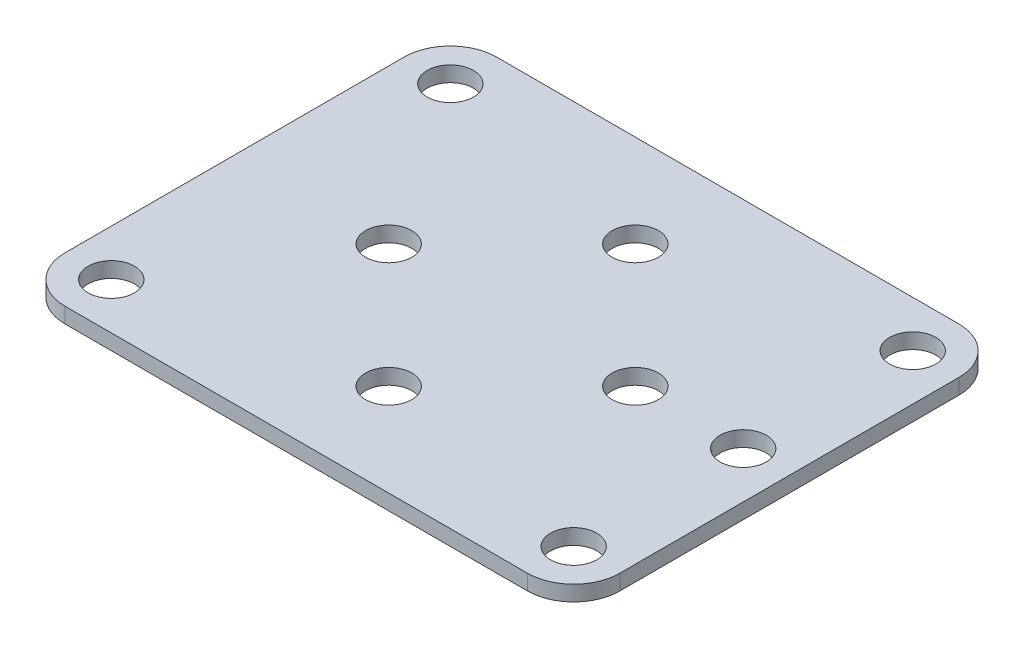
SolidWorks part; units mm, degrees
ref_plane "Front Plane" through (0, 0, 0) normal (0, 0, 1) x (1, 0, 0)
ref_plane "Top Plane" through (0, 0, 0) normal (0, 1, 0) x (1, 0, 0)
ref_plane "Right Plane" through (0, 0, 0) normal (1, 0, 0) x (0, 0, -1)
sketch "Sketch1" plane through (0, 0, 0) normal (0, 1, 0) x (1, 0, 0)
  line L0 (18, 28) -> (18, 0) construction
  line L1 (3, 0) -> (33, 0)
  line L2 (0, 3) -> (0, 25)
  line L3 (3, 28) -> (33, 28)
  line L4 (36, 3) -> (36, 25)
  line L5 (0, 14) -> (36, 14) construction
  circle A0 centre (3, 25) radius 1.5
  circle A1 centre (3, 3) radius 1.5
  circle A2 centre (33, 25) radius 1.5
  circle A3 centre (33, 3) radius 1.5
  arc A4 (0, 3) -> (3, 0) centre (3, 3) ccw
  arc A5 (33, 0) -> (36, 3) centre (33, 3) ccw
  arc A6 (36, 25) -> (33, 28) centre (33, 25) ccw
  arc A7 (0, 25) -> (3, 28) centre (3, 25) cw
  circle A8 centre (18, 22) radius 1.5
  circle A9 centre (18, 6) radius 1.5
  circle A10 centre (26, 14) radius 1.5
  circle A11 centre (10, 14) radius 1.5
  point P16 (0, 0)
  point P23 (0, 28)
  dimension "D4" = 30
  dimension "D7" = 3
  dimension "D8" = 8
  dimension "D9" = 8
  dimension "D1" = 22
  dimension "D2" = 28
  dimension "D3" = 3
  dimension "D5" = 3
  dimension "D6" = 3
extrude "Boss-Extrude1" add sketch "Sketch1" along normal blind 1
sketch "Sketch2" plane through (0, 1, 0) normal (0, 1, 0) x (1, 0, 0)
  line L0 (33, 28) -> (3, 28) construction
  line L2 (36, 3) -> (36, 25) construction
  circle A0 centre (33, 14) radius 1.5
  dimension "D1" = 14
  dimension "D2" = 3
extrude "Cut-Extrude1" cut sketch "Sketch2" against normal blind 10
